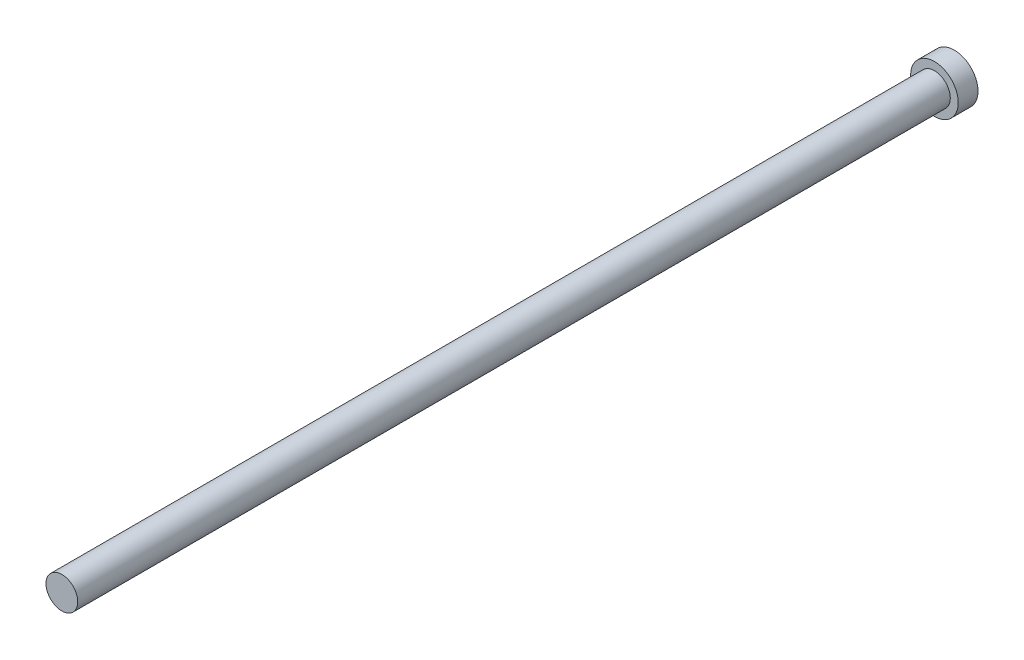
SolidWorks part; units mm, degrees
ref_plane "Front Plane" through (0, 0, 0) normal (0, 0, 1) x (1, 0, 0)
ref_plane "Top Plane" through (0, 0, 0) normal (0, 1, 0) x (1, 0, 0)
ref_plane "Right Plane" through (0, 0, 0) normal (1, 0, 0) x (0, 0, -1)
sketch "Sketch1" plane through (0, 0, 0) normal (0, 0, 1) x (1, 0, 0)
  circle A0 centre (0, 0) radius 1.016
  dimension "D1" = 2.032
extrude "Boss-Extrude1" add sketch "Sketch1" along normal blind 55.88
sketch "Sketch2" plane through (0, 0, 0) normal (0, 0, -1) x (-1, 0, 0)
  circle A0 centre (0, 0) radius 1.524
  dimension "D1" = 3.048
extrude "Boss-Extrude2" add sketch "Sketch2" along normal blind 1.27
